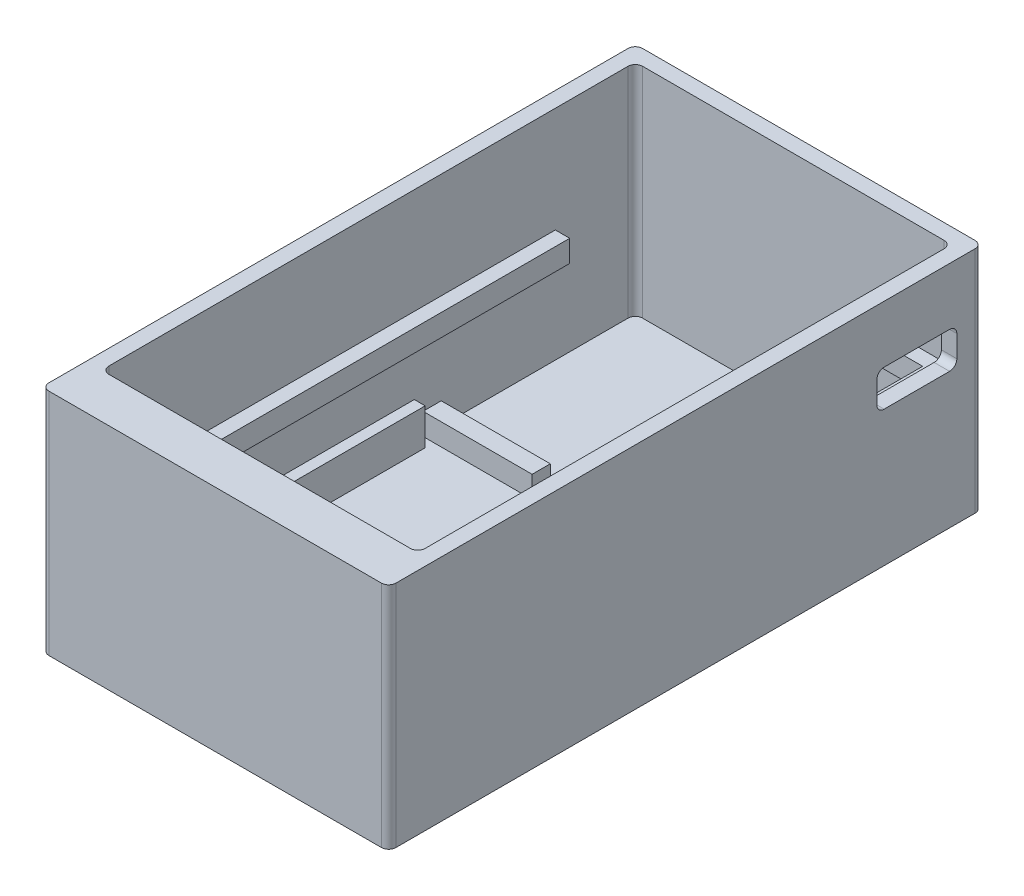
SolidWorks part; units mm, degrees
ref_plane "Front Plane" through (0, 0, 0) normal (0, 0, 1) x (1, 0, 0)
ref_plane "Top Plane" through (0, 0, 0) normal (0, 1, 0) x (1, 0, 0)
ref_plane "Right Plane" through (0, 0, 0) normal (1, 0, 0) x (0, 0, -1)
sketch "PCB Dimensions" plane through (0, 0, 0) normal (0, 1, 0) x (1, 0, 0)
  line L0 (0, 0) -> (-3.5355, 3.5355)
  line L1 (0, 0) -> (40.6457, 0)
  line L2 (0, 0) -> (0, -74.5657)
  line L3 (0, -74.5657) -> (40.6457, -74.5657)
  line L4 (40.6457, 0) -> (40.6457, -74.5657)
  line L5 (40.6457, -74.5657) -> (44.1812, -78.1012)
  line L6 (40.6457, 0) -> (44.1812, 3.5355)
  line L11 (0, -74.5657) -> (-3.5355, -78.1012)
  line L12 (44.1812, -78.1012) -> (-3.5355, -78.1012)
  line L13 (44.1812, -78.1012) -> (44.1812, 3.5355)
  line L14 (44.1812, 3.5355) -> (-3.5355, 3.5355)
  line L15 (-3.5355, -78.1012) -> (-3.5355, 3.5355)
extrude "Boss-Extrude3" add sketch "PCB Dimensions" along normal blind 1.5 contours L14 L15 L12 L13
sketch "Sketch5" plane through (0, 1.5, 0) normal (0, 1, 0) x (1, 0, 0)
  line L0 (-3.5355, 3.5355) -> (-1.4142, 1.4142)
  line L1 (-3.5355, 3.5355) -> (44.1812, 3.5355)
  line L2 (-3.5355, 3.5355) -> (-3.5355, -78.1012)
  line L7 (-3.5355, -78.1012) -> (44.1812, -78.1012)
  line L8 (44.1812, 3.5355) -> (44.1812, -78.1012)
  line L9 (44.1812, -78.1012) -> (42.0599, -71.9799)
  line L11 (-1.4142, 1.4142) -> (42.0599, 1.4142)
  line L12 (-1.4142, 1.4142) -> (-1.4142, -71.9799)
  line L13 (-1.4142, -71.9799) -> (42.0599, -71.9799)
  line L14 (42.0599, 1.4142) -> (42.0599, -71.9799)
extrude "Boss-Extrude5" add sketch "Sketch5" along normal blind 30
fillet "Fillet1" radius 1 8 edges at (42.0599, 16.5, 71.9799) (-3.5355, 15.75, 78.1012) (44.1812, 15.75, 78.1012) (44.1812, 15.75, -3.5355) (-3.5355, 15.75, -3.5355) (-1.4142, 16.5, 71.9799) (42.0599, 16.5, -1.4142) (-1.4142, 16.5, -1.4142)
sketch "Sketch9" plane through (0, 1.5, 0) normal (0, 1, 0) x (1, 0, 0)
  line L3 (0.0799, -70.9799) -> (-1.8581, -70.9799)
  line L9 (0.0799, -28.9799) -> (-1.8581, -28.9799)
  line L10 (-1.8581, -70.9799) -> (-1.8581, -28.9799)
  line L15 (42.5038, -70.9799) -> (42.5038, -28.9799)
  line L16 (40.5658, -28.9799) -> (42.5038, -28.9799)
  line L18 (40.5658, -70.9799) -> (42.5038, -70.9799)
  line L21 (0.0799, -28.9799) -> (0.0799, -70.9799)
  line L23 (40.5658, -28.9799) -> (40.5658, -70.9799)
sketch "Sketch7" plane through (0, 1.5, 0) normal (0, 1, 0) x (1, 0, 0)
  line L3 (-0.4992, 0.4992) -> (41.1449, 0.4992)
  line L4 (-0.4992, 0.4992) -> (-0.4992, -71.0649)
  line L5 (-0.4992, -71.0649) -> (41.1449, -71.0649)
  line L6 (41.1449, 0.4992) -> (41.1449, -71.0649)
extrude "Boss-Extrude6" add sketch "Sketch9" along normal blind 5 contours L21 L3 L10 L9 | L23 L18 L15 L16
sketch "Sketch14" plane through (0, 1.5, 0) normal (0, 1, 0) x (1, 0, 0)
  line L2 (-1.4142, -27.7799) -> (13.5858, -27.7799)
  line L3 (-1.4142, -27.7799) -> (-1.4142, -25.2799)
  line L4 (-1.4142, -25.2799) -> (13.5858, -25.2799)
  line L5 (13.5858, -27.7799) -> (13.5858, -25.2799)
  line L6 (27.0599, -27.7799) -> (27.0599, -25.2799)
  line L7 (42.0599, -25.2799) -> (27.0599, -25.2799)
  line L8 (42.0599, -27.7799) -> (42.0599, -25.2799)
  line L9 (42.0599, -27.7799) -> (27.0599, -27.7799)
extrude "Boss-Extrude7" add sketch "Sketch14" along normal blind 3
sketch "Sketch15" plane through (44.1812, 0, 0) normal (1, 0, 0) x (0, 0, -1)
  line L1 (-77.1012, 31.5) -> (-77.1012, 0) construction
  line L3 (2.5355, 0) -> (2.5355, 31.5) construction
  line L4 (-77.1012, 14) -> (2.5355, 14)
  line L5 (-77.1012, 14) -> (-77.1012, 17)
  line L6 (-77.1012, 17) -> (2.5355, 17)
  line L7 (2.5355, 14) -> (2.5355, 17)
  line M8 (-77.1012, 31.5) -> (-77.1012, 0)
  line M10 (2.5355, 0) -> (2.5355, 31.5)
extrude "Boss-Extrude8" add sketch "Sketch15" against normal blind 46 contours L6 L4 M8 M10
sketch "Sketch17" plane through (0, 17, 0) normal (0, 1, 0) x (1, 0, 0)
  line L3 (40.0842, -63.5437) -> (0.5614, -63.5437)
  line L4 (40.0842, -63.5437) -> (40.0842, -0.5614)
  line L5 (40.0842, -0.5614) -> (0.5614, -0.5614)
  line L6 (0.5614, -63.5437) -> (0.5614, -0.5614)
extrude "Cut-Extrude1" cut sketch "Sketch17" against normal blind 3 contours L5 L6 L3 L4
sketch "Sketch18" plane through (0, 17, 0) normal (0, 1, 0) x (1, 0, 0)
  line L0 (-1.4142, -70.9799) -> (-1.4142, 0.4142) construction
  line L1 (-1.4142, -9.5858) -> (28.5858, -9.5858)
  line L4 (28.5858, -9.5858) -> (28.5858, 1.4142)
  line L5 (-0.4142, 1.4142) -> (41.0599, 1.4142) construction
  line L6 (-0.4142, 1.4142) -> (28.5858, 1.4142)
  line L7 (-1.4142, 0.4142) -> (-1.4142, -9.5858)
  arc A0 (-1.4142, 0.4142) -> (-0.4142, 1.4142) centre (-0.4142, 0.4142) cw
extrude "Cut-Extrude2" cut sketch "Sketch18" against normal blind 3
sketch "Sketch19" plane through (44.1812, 0, 0) normal (1, 0, 0) x (0, 0, -1)
  line L0 (2.5355, 0) -> (2.5355, 17)
  line L1 (2.5355, 0) -> (2.5355, 31.5) construction
  line L2 (0.0355, 23.65) -> (0.0355, 18.65)
  line L11 (0.0355, 18.65) -> (-10.9645, 18.65)
  line L13 (0.0355, 23.65) -> (-10.9645, 23.65)
  line L14 (-10.9645, 18.65) -> (-10.9645, 23.65)
extrude "Cut-Extrude3" cut sketch "Sketch19" against normal blind 10 contours L13 L14 L11 L2
fillet "Fillet2" radius 1 4 edges at (43.1205, 18.65, 10.9645) (43.1205, 18.65, -0.0355) (43.1205, 23.65, -0.0355) (43.1205, 23.65, 10.9645)
scale "Scale1" bodies to scale 113 scale about centroid uniform scaling yes scale factor 0.99
